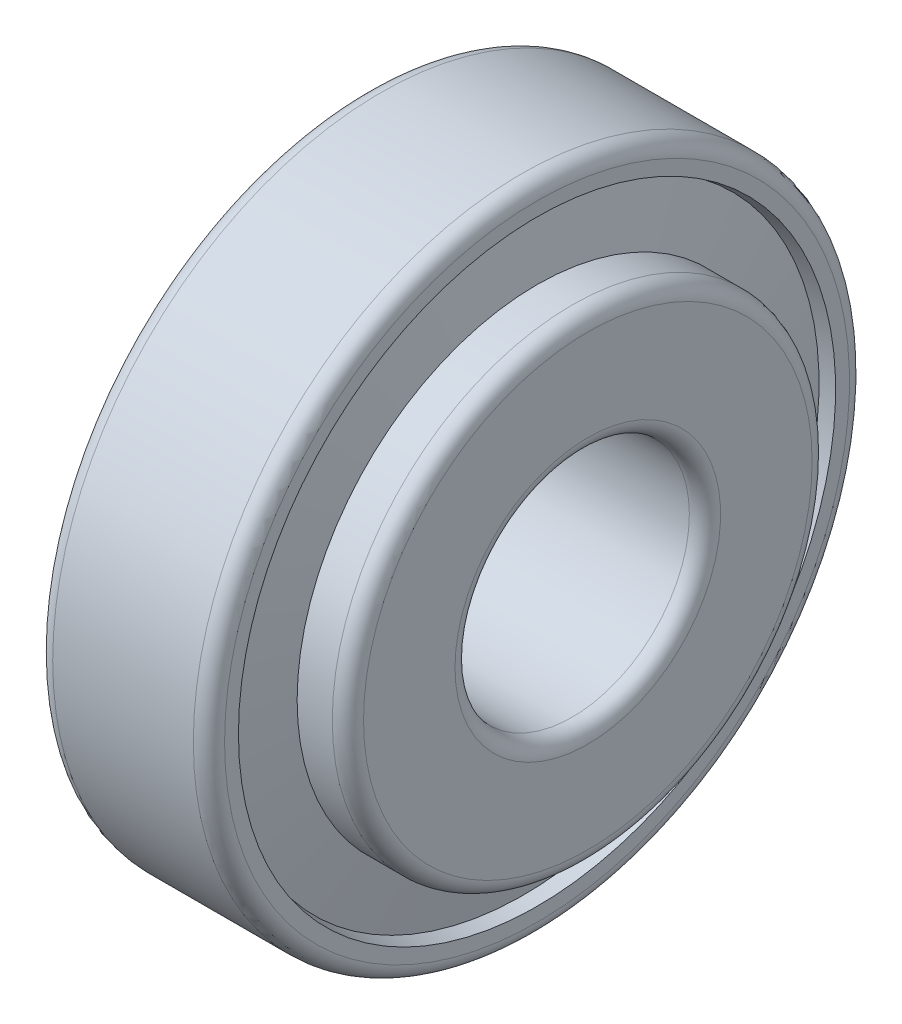
SolidWorks part; units mm, degrees
material "AISI Тип A2 Инструментальная сталь"
ref_plane "Спереди" through (0, 0, 0) normal (0, 0, 1) x (1, 0, 0)
ref_plane "Сверху" through (0, 0, 0) normal (0, 1, 0) x (1, 0, 0)
ref_plane "Справа" through (0, 0, 0) normal (1, 0, 0) x (0, 0, -1)
sketch "Эскиз1" plane through (0, 0, 0) normal (0, 0, 1) x (1, 0, 0)
  line L20 (-882.5277, 0) -> (43243.8573, 0) construction
  line L33 (2.0122, 17.0889) -> (0, 16.636)
  line L34 (0, 16.636) -> (0, 20)
  line L35 (1, 21) -> (10, 21)
  line L36 (11, 20) -> (11, 19.1117)
  line L37 (11, 19.1117) -> (10.1334, 18.9166)
  line L38 (2.0122, 17.0889) -> (10.1334, 18.9166) construction
  line L39 (2.7744, 13.0772) -> (1.25, 13.0772)
  line L40 (1.25, 13.0772) -> (1.25, 8.5)
  line L41 (2.25, 7.5) -> (13.25, 7.5)
  line L42 (14.25, 8.5) -> (14.25, 14.3554)
  line L43 (13.25, 15.3554) -> (11, 15.3554)
  line L44 (11, 15.3554) -> (11, 14.3554)
  line L45 (2.7744, 13.0772) -> (11, 14.3554) construction
  line L46 (11, 14.3554) -> (10.1334, 18.9166)
  line L47 (2.7744, 13.0772) -> (2.0122, 17.0889)
  line L48 (2.3933, 15.0831) -> (10.5667, 16.636) construction
  line L49 (0, 16.636) -> (10.5667, 16.636) construction
  line L50 (2.0122, 17.0889) -> (2.0122, 13.0772) construction
  arc A0 (0, 20) -> (1, 21) centre (1, 20) cw
  arc A1 (10, 21) -> (11, 20) centre (10, 20) cw
  arc A2 (1.25, 8.5) -> (2.25, 7.5) centre (2.25, 8.5) ccw
  arc A3 (14.25, 8.5) -> (13.25, 7.5) centre (13.25, 8.5) cw
  arc A4 (13.25, 15.3554) -> (14.25, 14.3554) centre (13.25, 14.3554) cw
  point P12 (10.5667, 16.636)
  dimension "гост r1" = 1
  dimension "гост r2" = 1
  dimension "гост DD" = 42
  dimension "гост B" = 13
  dimension "гост C" = 11
  dimension "гост T" = 14.25
  dimension "гост E" = 33.272
  dimension "гост d" = 15
  dimension "гост alfa" = 10.758
revolve "Повернуть1" add sketch "Эскиз1" angle 360 about L20
